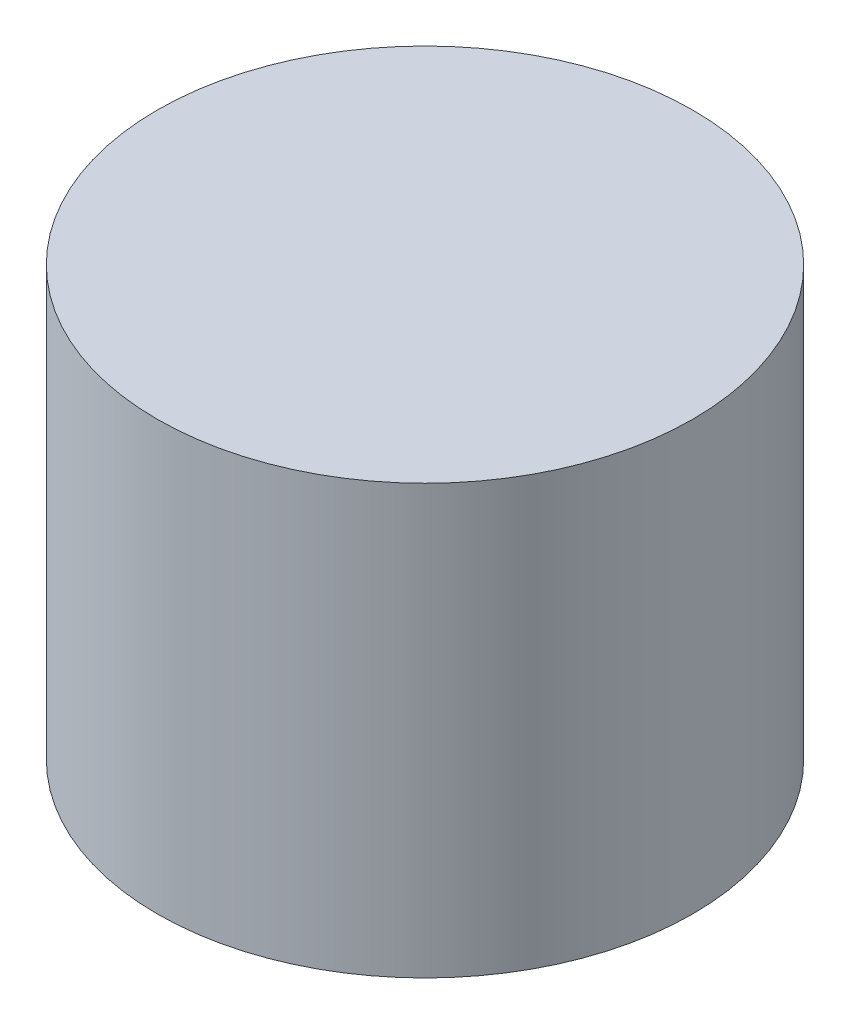
SolidWorks part; units mm, degrees
ref_plane "Спереди" through (0, 0, 0) normal (0, 0, 1) x (1, 0, 0)
ref_plane "Сверху" through (0, 0, 0) normal (0, 1, 0) x (1, 0, 0)
ref_plane "Справа" through (0, 0, 0) normal (1, 0, 0) x (0, 0, -1)
sketch "Sketch1" plane through (0, 0, 0) normal (0, 1, 0) x (1, 0, 0)
  circle A0 centre (0, 0) radius 3
  dimension "D1" = 6
extrude "Boss-Extrude1" add sketch "Sketch1" along normal blind 4.8
